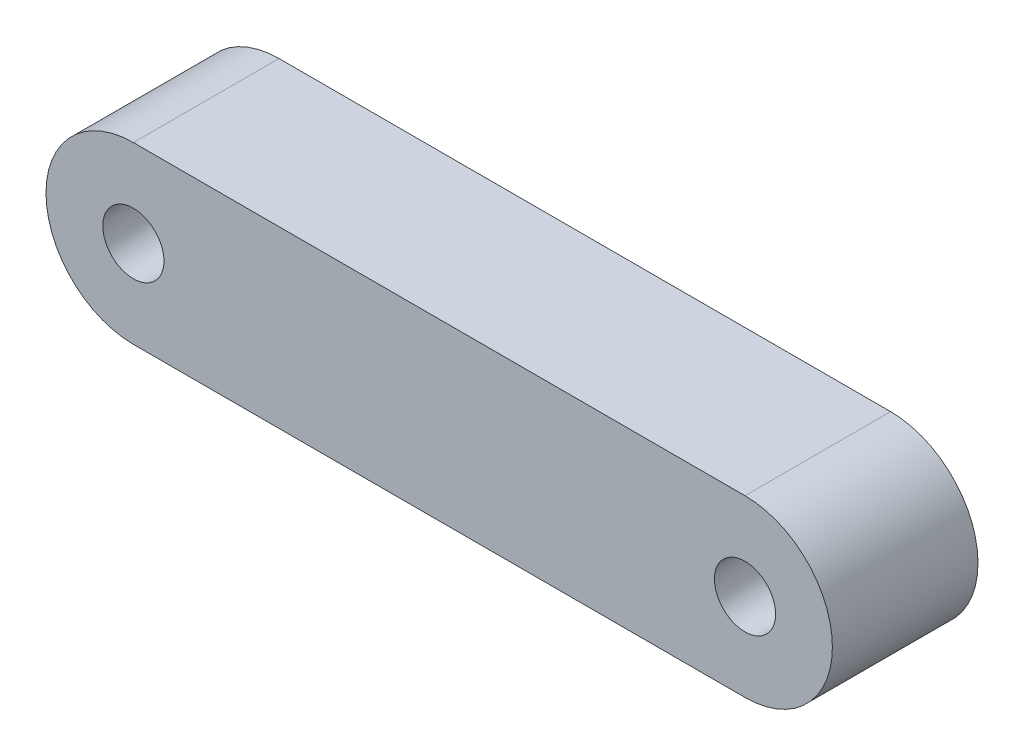
SolidWorks part; units mm, degrees
ref_plane "Front Plane" through (0, 0, 0) normal (0, 0, 1) x (1, 0, 0)
ref_plane "Top Plane" through (0, 0, 0) normal (0, 1, 0) x (1, 0, 0)
ref_plane "Right Plane" through (0, 0, 0) normal (1, 0, 0) x (0, 0, -1)
sketch "Sketch1" plane through (0, 0, 0) normal (0, 0, 1) x (1, 0, 0)
  line L0 (0, 0) -> (35, 0) construction
  line L1 (0, 5) -> (35, 5)
  line L2 (35, -5) -> (0, -5)
  arc A0 (0, 5) -> (0, -5) centre (0, 0) ccw
  arc A1 (35, -5) -> (35, 5) centre (35, 0) ccw
  circle A2 centre (0, 0) radius 1.75
  circle A3 centre (35, 0) radius 1.75
  dimension "D2" = 10
  dimension "D3" = 10
  dimension "D4" = 3.5
  dimension "D5" = 3.5
  dimension "D1" = 35
extrude "Boss-Extrude1" add sketch "Sketch1" along normal blind 8.3333
